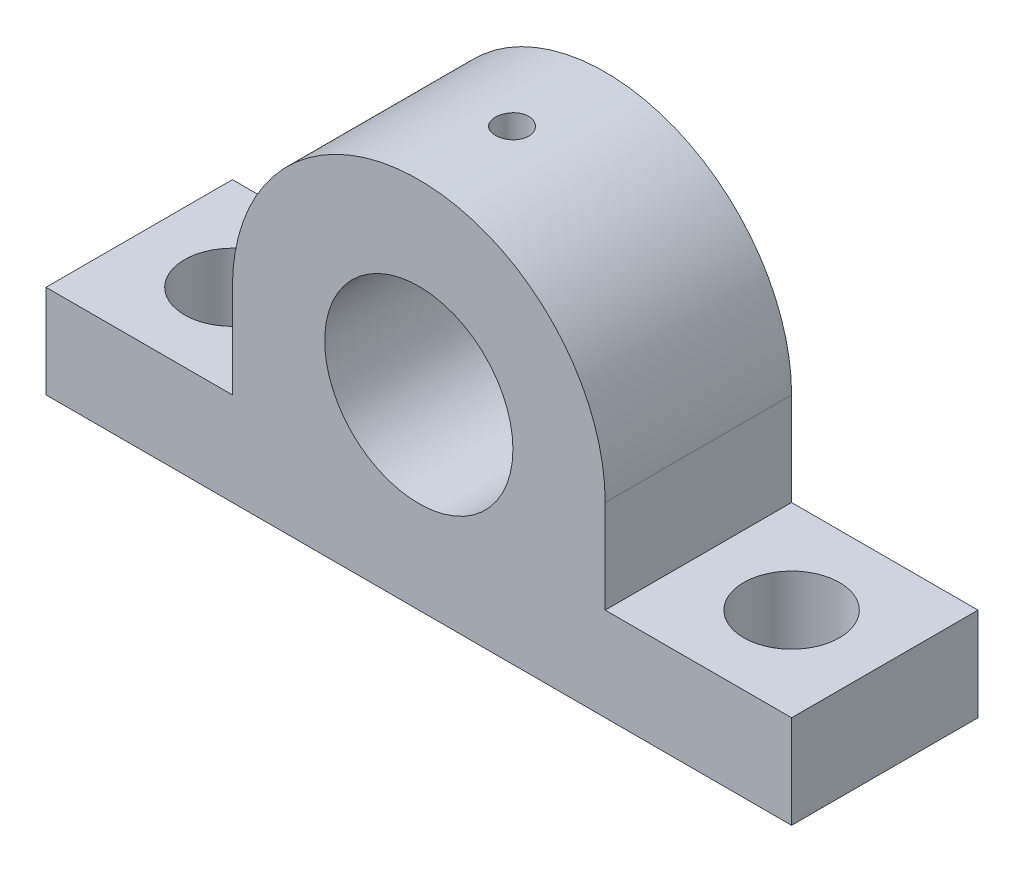
SolidWorks part; units mm, degrees
ref_plane "Front Plane" through (0, 0, 0) normal (0, 0, 1) x (1, 0, 0)
ref_plane "Top Plane" through (0, 0, 0) normal (0, 1, 0) x (1, 0, 0)
ref_plane "Right Plane" through (0, 0, 0) normal (1, 0, 0) x (0, 0, -1)
sketch "Sketch1" plane through (0, 0, 0) normal (0, 0, 1) x (1, 0, 0)
  line L0 (0, 0) -> (0, 12.7) construction
  line L2 (12.7, 12.7) -> (12.7, 6.35)
  line L3 (12.7, 6.35) -> (25.4, 6.35)
  line L4 (25.4, 6.35) -> (25.4, 0)
  line L5 (25.4, 0) -> (-25.4, 0)
  line L6 (-25.4, 0) -> (-25.4, 6.35)
  line L7 (-25.4, 6.35) -> (-12.7, 6.35)
  line L8 (-12.7, 6.35) -> (-12.7, 12.7)
  circle A0 centre (0, 12.7) radius 6.4135
  arc A1 (-12.7, 12.7) -> (12.7, 12.7) centre (0, 12.7) cw
  dimension "D5" = 12.827
  dimension "D1" = 50.8
  dimension "D2" = 6.35
  dimension "D3" = 25.4
  dimension "D4" = 25.4
extrude "Boss-Extrude1" add sketch "Sketch1" along normal blind 12.7
sketch "Sketch2" plane through (0, 6.35, 0) normal (0, 1, 0) x (1, 0, 0)
  line L0 (0, 0) -> (0, -4.6153) construction
  line L1 (12.7, -12.7) -> (25.4, 0) construction
  line L2 (-55, 0) -> (55, 0) construction
  line L3 (25.4, -12.7) -> (25.4, 0) construction
  circle A0 centre (19.05, -6.35) radius 3.2639
  circle A1 centre (-19.05, -6.35) radius 3.2639
  point P14 (0, 0)
  point P15 (19.05, -6.35)
  dimension "D1" = 6.5278
extrude "Cut-Extrude1" cut sketch "Sketch2" against normal through all
hole_wizard "#4-40 Tapped Hole1" positions "3DSketch2" profile "Sketch6" tap size "#4-40" standard "ANSI Inch"
sketch3d "3DSketch2"
  line L0 (0, 25.4, 0) -> (0, 25.4, 12.7) construction
  arc A0 (12.7, 12.7, 0) -> (-12.7, 12.7, 0) centre (0, 12.7, 0) ccw construction
  arc A1 (12.7, 12.7, 12.7) -> (-12.7, 12.7, 12.7) centre (0, 12.7, 12.7) ccw construction
  point P0 (0, 25.4, 6.35)
  point P9 (0, 12.7, 12.7)
  point P13 (0, 12.7, 25.4)
  point P16 (0, 0, 0)
  point P17 (1.3603, 25.3269, 6.0949)
  point P18 (-0.8889, 25.3689, 0)
  point P19 (1.0003, 25.3605, 0)
sketch "Sketch6" plane through (0, 25.4, 6.35) normal (1, 0, 0) x (0, 0, 1)
  line L0 (0, 0) -> (0, 8.2992)
  line L1 (0, 8.2992) -> (1.1303, 7.62)
  line L2 (1.1303, 7.62) -> (1.1303, 0)
  line L5 (1.1303, 0) -> (0, 0)
  line L10 (0, 8.2992) -> (-1.1303, 7.62) construction
  line L11 (0, -6.35) -> (0, 107.95) construction
  dimension "Tap Drill Dia." = 2.2606
  dimension "Tap Drill Depth" = 7.62
  dimension "Drill Angle" = 118
cosmetic thread "Hole Thread1" parameters "D1"=5.588, "D2"=2.8448
